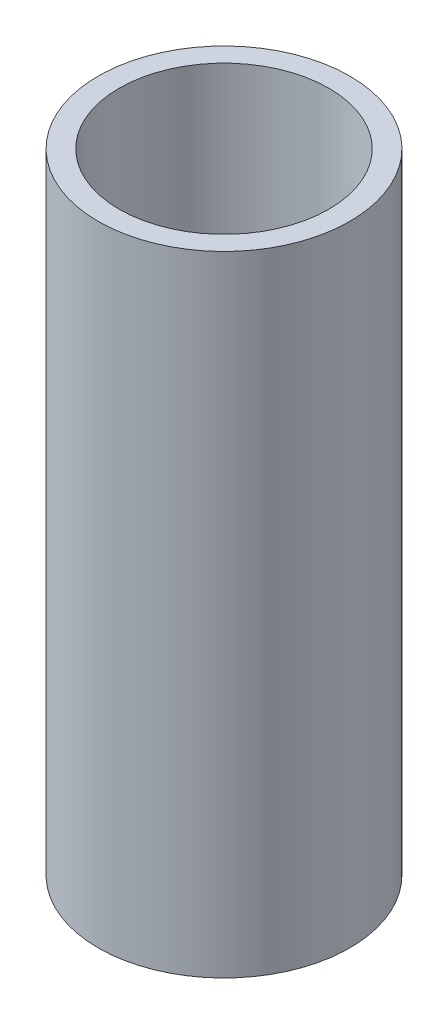
SolidWorks part; units mm, degrees
ref_plane "Alzado" through (0, 0, 0) normal (0, 0, 1) x (1, 0, 0)
ref_plane "Planta" through (0, 0, 0) normal (0, 1, 0) x (1, 0, 0)
ref_plane "Vista lateral" through (0, 0, 0) normal (1, 0, 0) x (0, 0, -1)
sketch "Croquis1" plane through (0, 0, 0) normal (0, 1, 0) x (1, 0, 0)
  circle A0 centre (0, 0) radius 3
  circle A1 centre (0, 0) radius 2.5
  dimension "D1" = 5
  dimension "D2" = 6
extrude "Saliente-Extruir1" add sketch "Croquis1" along normal blind 15
